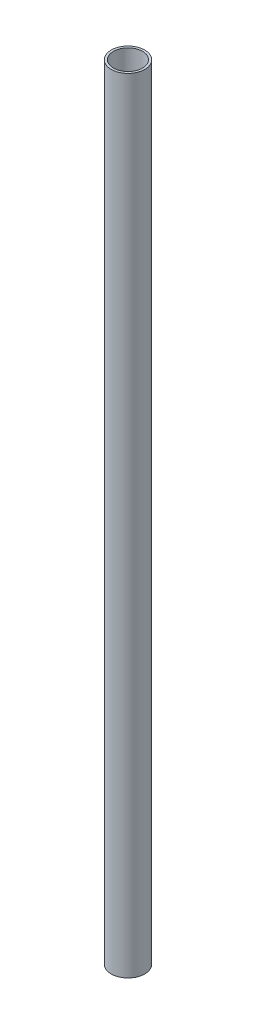
SolidWorks part; units mm, degrees
material "Thornel Mat VMA"
ref_plane "Front Plane" through (0, 0, 0) normal (0, 0, 1) x (1, 0, 0)
ref_plane "Top Plane" through (0, 0, 0) normal (0, 1, 0) x (1, 0, 0)
ref_plane "Right Plane" through (0, 0, 0) normal (1, 0, 0) x (0, 0, -1)
sketch "Sketch1" plane through (0, 0, 0) normal (0, 1, 0) x (1, 0, 0)
  circle A0 centre (0, 0) radius 15
  circle A1 centre (0, 0) radius 13
  dimension "D1" = 30
  dimension "D2" = 26
extrude "Boss-Extrude1" add sketch "Sketch1" along normal blind 700
